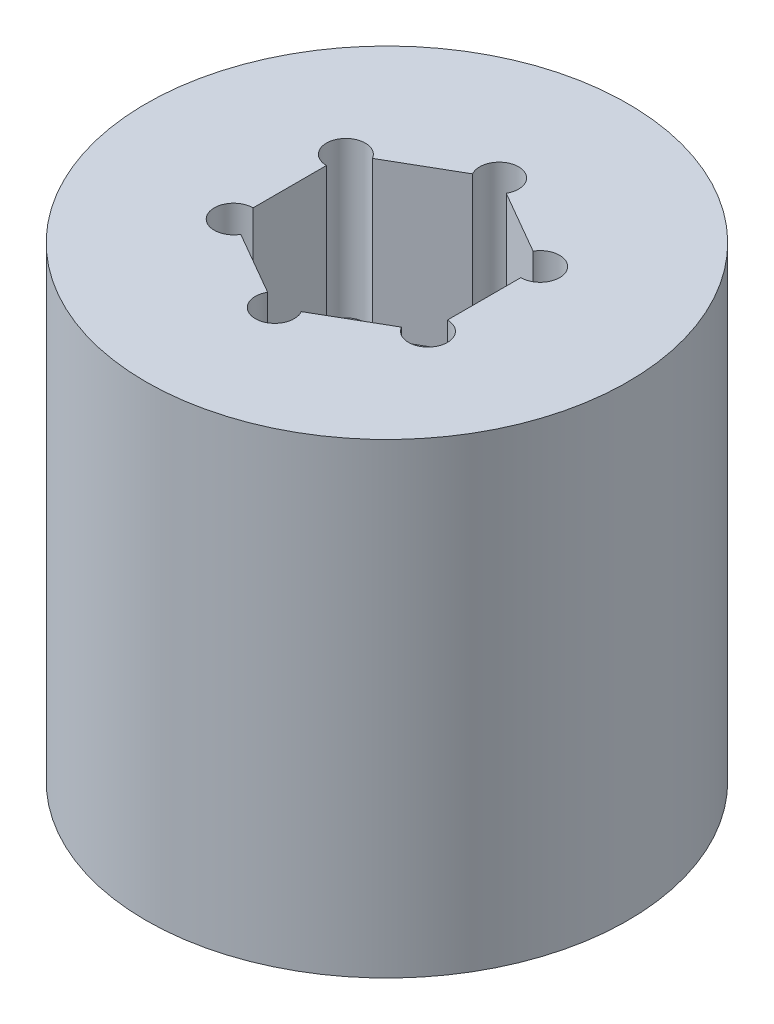
SolidWorks part; units mm, degrees
ref_plane "Front Plane" through (0, 0, 0) normal (0, 0, 1) x (1, 0, 0)
ref_plane "Top Plane" through (0, 0, 0) normal (0, 1, 0) x (1, 0, 0)
ref_plane "Right Plane" through (0, 0, 0) normal (1, 0, 0) x (0, 0, -1)
sketch "Sketch3" plane through (0, 0, 0) normal (0, 1, 0) x (1, 0, 0)
  circle A0 centre (0, 0) radius 19.685
  dimension "D1" = 39.37
extrude "Boss-Extrude1" add sketch "Sketch3" along normal mid plane 38.1
sketch "Sketch4" plane through (0, -19.05, 0) normal (0, -1, 0) x (1, 0, 0)
  line L1 (-12.7, -12.7) -> (12.7, -12.7)
  line L2 (-12.7, -12.7) -> (-12.7, 12.7)
  line L3 (-12.7, 12.7) -> (12.7, 12.7)
  line L4 (12.7, -12.7) -> (12.7, 12.7)
  line L5 (-12.7, -12.7) -> (12.7, 12.7) construction
  line L6 (-12.7, 12.7) -> (12.7, -12.7) construction
  circle A0 centre (12.7, -12.7) radius 1.5875
  circle A1 centre (-12.7, -12.7) radius 1.5875
  circle A2 centre (-12.7, 12.7) radius 1.5875
  circle A3 centre (12.7, 12.7) radius 1.5875
  point P0 (0, 0)
  dimension "D1" = 3.175
  dimension "D2" = 25.4
extrude "Cut-Extrude1" cut sketch "Sketch4" against normal blind 19.05 contours A3 L3 A2 L2 A1 L1 A0 L4 | L1 A1 L2 | L2 A2 L3 | L3 A3 L4 | L4 A0 L1 | L5 A1 L1 L2 | L3 A2 L5 L2 | L4 A3 L5 L3 | L5 A0 L4 L1 | L5 A1 | L5 A2 | L5 A3 | L5 A0
sketch "Sketch5" plane through (0, 19.05, 0) normal (0, 1, 0) x (1, 0, 0)
  line L1 (0, 9.1654) -> (-7.9375, 4.5827)
  line L2 (-7.9375, 4.5827) -> (-7.9375, -4.5827)
  line L3 (-7.9375, -4.5827) -> (0, -9.1654)
  line L4 (0, -9.1654) -> (7.9375, -4.5827)
  line L5 (7.9375, -4.5827) -> (7.9375, 4.5827)
  line L6 (7.9375, 4.5827) -> (0, 9.1654)
  circle A0 centre (0, 0) radius 7.9375 construction
  circle A1 centre (0, 9.1654) radius 1.5875
  circle A2 centre (-7.9375, 4.5827) radius 1.5875
  circle A3 centre (-7.9375, -4.5827) radius 1.5875
  circle A4 centre (0, -9.1654) radius 1.5875
  circle A5 centre (7.9375, -4.5827) radius 1.5875
  circle A6 centre (7.9375, 4.5827) radius 1.5875
  dimension "D2" = 3.175
  dimension "D1" = 15.875
extrude "Cut-Extrude2" cut sketch "Sketch5" against normal blind 12.7 contours A6 L6 A1 L1 A2 L2 A3 L3 A4 L4 A5 L5 | L3 A3 L2 | L2 A3 L3 | L3 A4 L4 | L4 A4 L3 | L4 A5 L5 | L5 A5 L4 | L6 A6 L5 | L5 A6 L6 | L6 A1 L1 | L1 A1 L6 | L1 A2 L2 | L2 A2 L1
